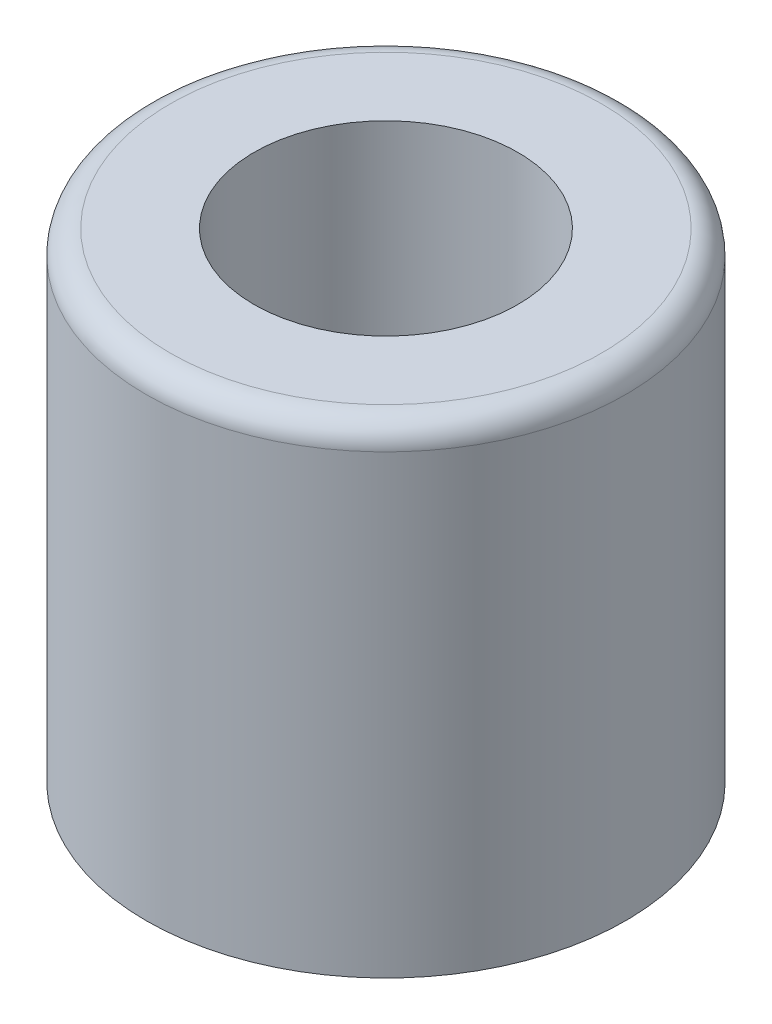
SolidWorks part; units mm, degrees
ref_plane "Front Plane" through (0, 0, 0) normal (0, 0, 1) x (1, 0, 0)
ref_plane "Top Plane" through (0, 0, 0) normal (0, 1, 0) x (1, 0, 0)
ref_plane "Right Plane" through (0, 0, 0) normal (1, 0, 0) x (0, 0, -1)
sketch "Sketch1" plane through (0, 0, 0) normal (0, 1, 0) x (1, 0, 0)
  circle A0 centre (0, 0) radius 5
  circle A1 centre (0, 0) radius 2.75
extrude "Boss-Extrude1" add sketch "Sketch1" along normal blind 10 contours A1 | A0
fillet "Fillet3" radius 0.5 1 edges at (0, 10, 5)
